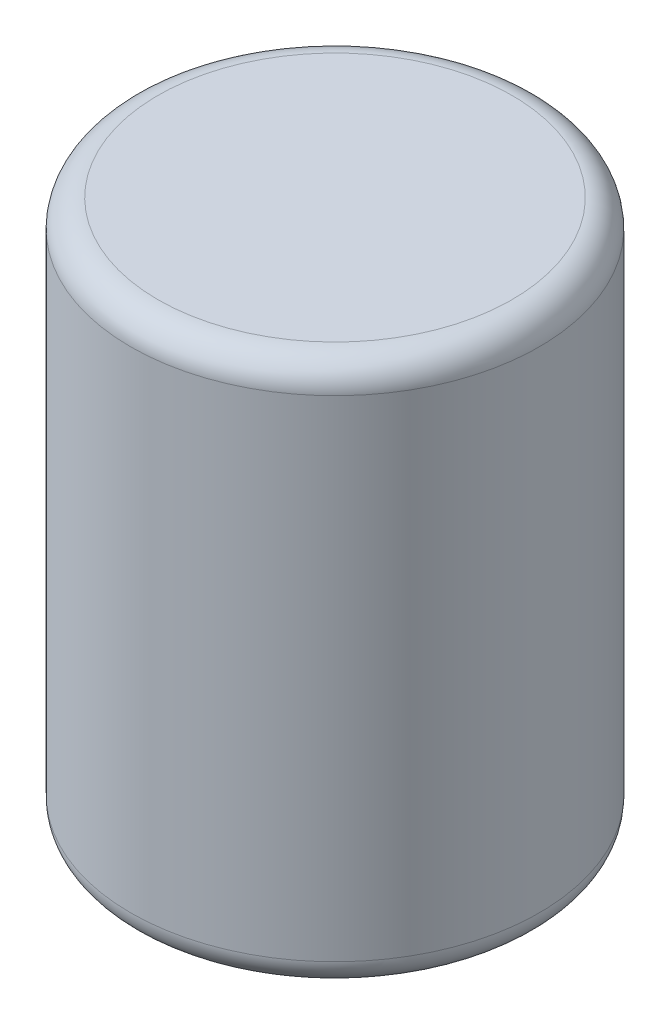
SolidWorks part; units mm, degrees
ref_plane "Plano frontal" through (0, 0, 0) normal (0, 0, 1) x (1, 0, 0)
ref_plane "Plano superior" through (0, 0, 0) normal (0, 1, 0) x (1, 0, 0)
ref_plane "Plano direito" through (0, 0, 0) normal (1, 0, 0) x (0, 0, -1)
sketch "Esboço1" plane through (0, 0, 0) normal (0, 1, 0) x (1, 0, 0)
  circle A0 centre (0, 0) radius 750
extrude "Ressalto-extrusão1" add sketch "Esboço1" along normal blind 2000
fillet "Filete1" radius 100 2 edges at (0, 0, 750) (0, 2000, 750)
